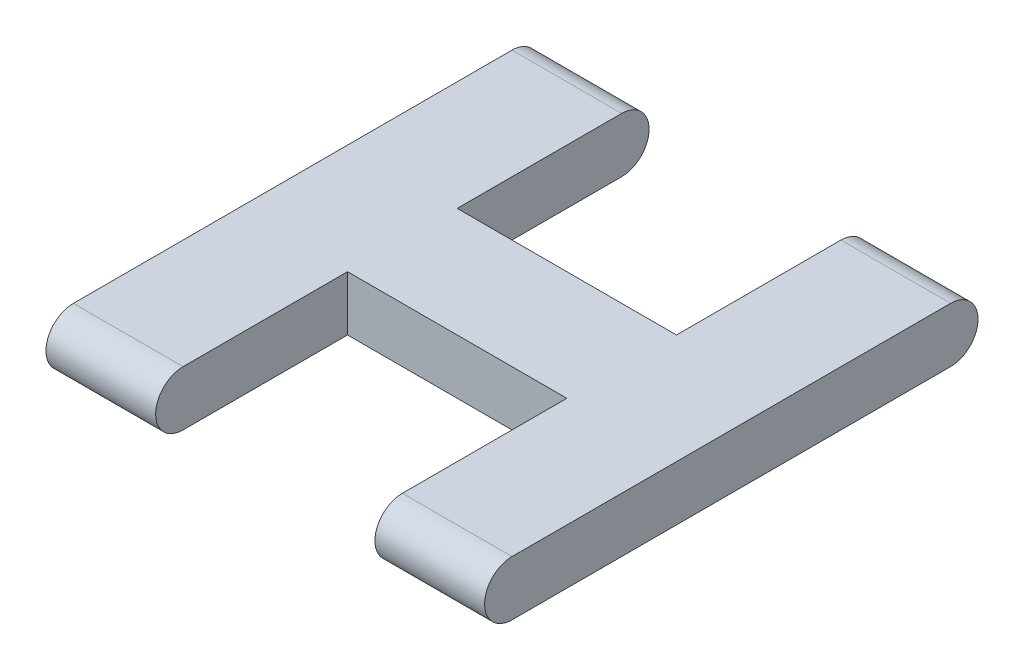
SolidWorks part; units mm, degrees
ref_plane "Front" through (0, 0, 0) normal (0, 0, 1) x (1, 0, 0)
ref_plane "Top" through (0, 0, 0) normal (0, 1, 0) x (1, 0, 0)
ref_plane "Right" through (0, 0, 0) normal (1, 0, 0) x (0, 0, -1)
sketch "草图1" plane through (0, 0, 0) normal (1, 0, 0) x (0, 0, -1)
  line L0 (-8, 0) -> (8, 0) construction
  line L1 (-8, 1) -> (8, 1)
  line L2 (-8, -1) -> (8, -1)
  arc A0 (-8, 1) -> (-8, -1) centre (-8, 0) ccw
  arc A1 (8, -1) -> (8, 1) centre (8, 0) ccw
  point P2 (0, 0)
extrude "凸台-拉伸1" add sketch "草图1" along normal blind 16
sketch "草图2" plane through (0, 1, 0) normal (0, 1, 0) x (1, 0, 0)
  line L0 (8, 9) -> (8, -9) construction
  line L1 (16, 9) -> (0, 9) construction
  line L2 (0, -9) -> (16, -9) construction
  line L3 (16, -8) -> (0, -8) construction
  line L4 (4, 11.7088) -> (12, 11.7088)
  line L5 (4, 11.7088) -> (4, 2)
  line L6 (4, 2) -> (12, 2)
  line L7 (12, 11.7088) -> (12, 2)
  line L8 (12, -11.6503) -> (4, -11.6503)
  line L9 (12, -11.6503) -> (12, -2)
  line L10 (12, -2) -> (4, -2)
  line L11 (4, -11.6503) -> (4, -2)
  line L12 (16, 8) -> (0, 8) construction
  dimension "D1" = 8
  dimension "D2" = 4
  dimension "D3" = 6
  dimension "D4" = 8
  dimension "D5" = 4
  dimension "D6" = 6
extrude "切除-拉伸1" cut sketch "草图2" against normal blind 14
